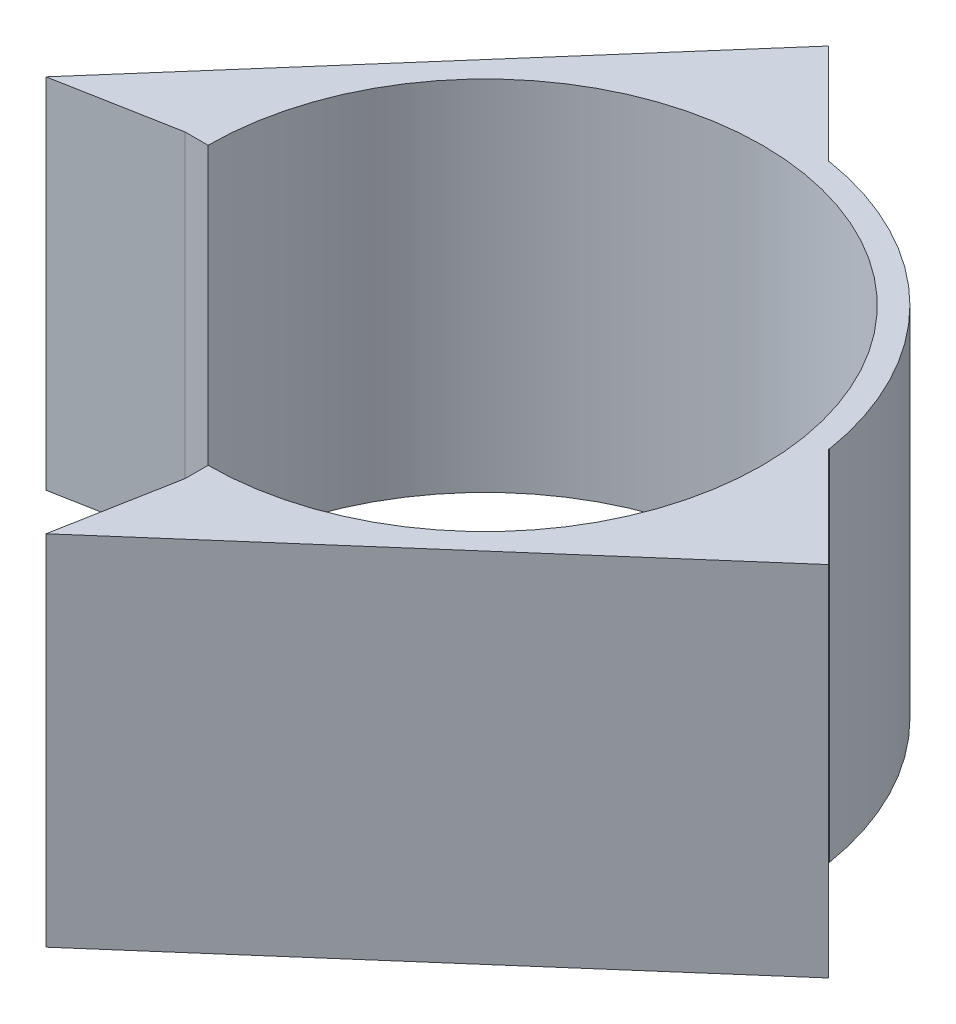
SolidWorks part; units mm, degrees
ref_plane "Front Plane" through (0, 0, 0) normal (0, 0, 1) x (1, 0, 0)
ref_plane "Top Plane" through (0, 0, 0) normal (0, 1, 0) x (1, 0, 0)
ref_plane "Right Plane" through (0, 0, 0) normal (1, 0, 0) x (0, 0, -1)
sketch "Sketch1" plane through (0, 0, 0) normal (0, 1, 0) x (1, 0, 0)
  line L0 (-52.0001, -0.0001) -> (-48, -0.0001)
  line L1 (0, -48) -> (0, -52.0001)
  line L12 (-72.2865, -3.7682) -> (-9.1853, 68.5798)
  line L16 (-3.7681, -72.2866) -> (68.5798, -9.1852)
  line L20 (68.5798, -9.1852) -> (75.6521, -2.1129)
  line L21 (-9.1853, 68.5798) -> (-2.1129, 75.6521)
  line L22 (51.3785, 8.0161) -> (58.4508, 15.0884)
  line L23 (58.4508, 15.0884) -> (75.6521, -2.1129)
  line L24 (8.016, 51.3785) -> (15.0884, 58.4508)
  line L25 (15.0884, 58.4508) -> (-2.1129, 75.6521)
  line L26 (0, -52.0001) -> (-3.7681, -72.2866)
  line L27 (-72.2865, -3.7682) -> (-52.0001, -0.0001)
  arc A0 (-48, -0.0001) -> (0, -48) centre (0, 0) cw
  arc A1 (8.016, 51.3785) -> (51.3785, 8.0161) centre (0, 0) cw
extrude "Boss-Extrude1" add sketch "Sketch1" along normal blind 62
sketch "Sketch3" plane through (38.8825, 0, 38.8825) normal (0.7071, 0, 0.7071) x (0.7071, 0, -0.7071)
  line L1 (56.9983, 80.2781) -> (56.9983, 0)
  line L2 (41.9983, 0) -> (56.9983, 0)
  line L9 (41.9983, 62) -> (41.9983, 0) construction
  line L11 (41.9983, 80.2781) -> (56.9983, 80.2781)
  line L14 (41.9983, 80.2781) -> (41.9983, 0)
  point P0 (0, 0)
extrude "Cut-Extrude1" cut sketch "Sketch3" against normal blind 24.5
sketch "Sketch4" plane through (-38.8825, 0, -38.8825) normal (-0.7071, 0, -0.7071) x (-0.7071, 0, 0.7071)
  line L3 (-60.1258, 0) -> (-41.9983, 0)
  line L6 (-41.9983, 62) -> (-41.9983, 0) construction
  line L11 (-41.9983, 69.7097) -> (-41.9983, 0)
  line L13 (-60.1258, 69.7097) -> (-41.9983, 69.7097)
  line L14 (-60.1258, 69.7097) -> (-60.1258, 0)
extrude "Cut-Extrude2" cut sketch "Sketch4" against normal blind 24.5
equation "\"5.6cmmm\"=10"
